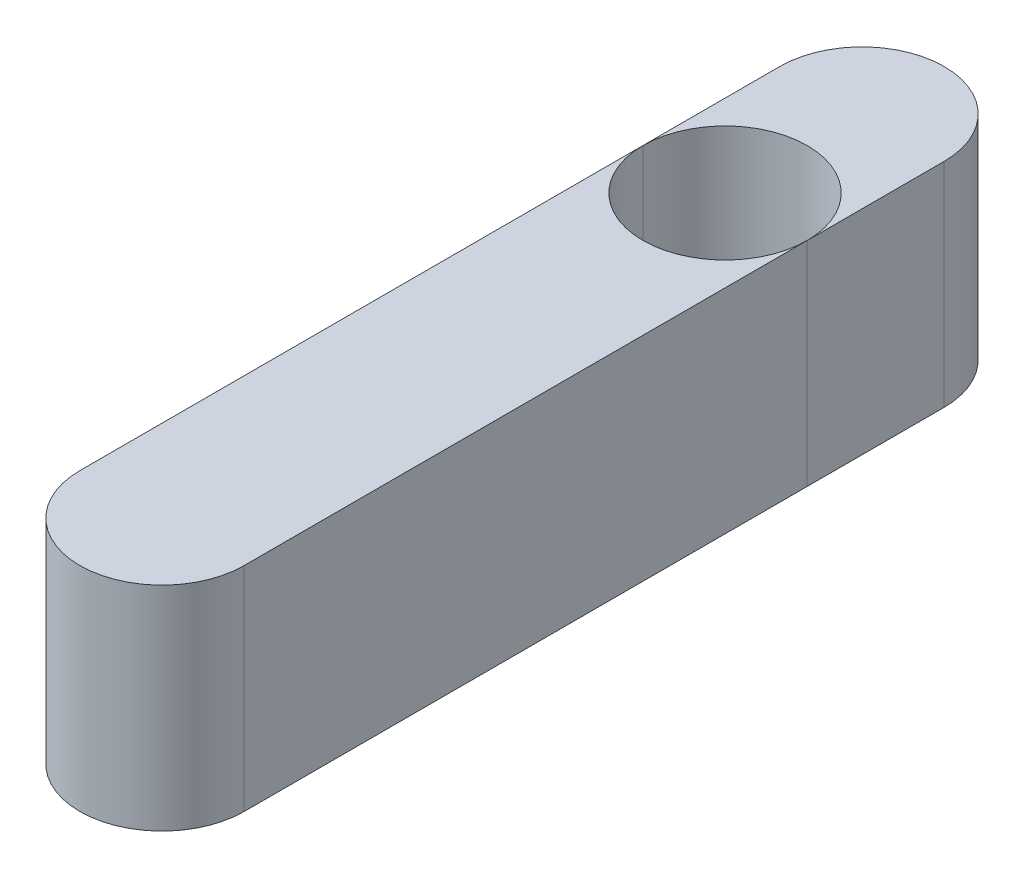
SolidWorks part; units mm, degrees
ref_plane "Front Plane" through (0, 0, 0) normal (0, 0, 1) x (1, 0, 0)
ref_plane "Top Plane" through (0, 0, 0) normal (0, 1, 0) x (1, 0, 0)
ref_plane "Right Plane" through (0, 0, 0) normal (1, 0, 0) x (0, 0, -1)
sketch "Sketch1" plane through (0, 0, 0) normal (0, 1, 0) x (1, 0, 0)
  line L0 (0, 0) -> (0, 23) construction
  line L1 (-2.7, 0) -> (-2.7, 23)
  line L2 (2.7, 0) -> (2.7, 23)
  arc A0 (-2.7, 0) -> (2.7, 0) centre (0, 0) ccw
  arc A1 (2.7, 23) -> (-2.7, 23) centre (0, 23) ccw
  point P3 (0, 11.5)
  dimension "D1" = 23
  dimension "D2" = 5.4
extrude "Boss-Extrude1" add sketch "Sketch1" along normal blind 7
sketch "Sketch2" plane through (0, 7, 0) normal (0, 1, 0) x (1, 0, 0)
  line L0 (0, 0) -> (0, 18.5) construction
  circle A0 centre (0, 18.5) radius 2.7
  dimension "D1" = 18.5
extrude "Cut-Extrude1" cut sketch "Sketch2" against normal blind 7
